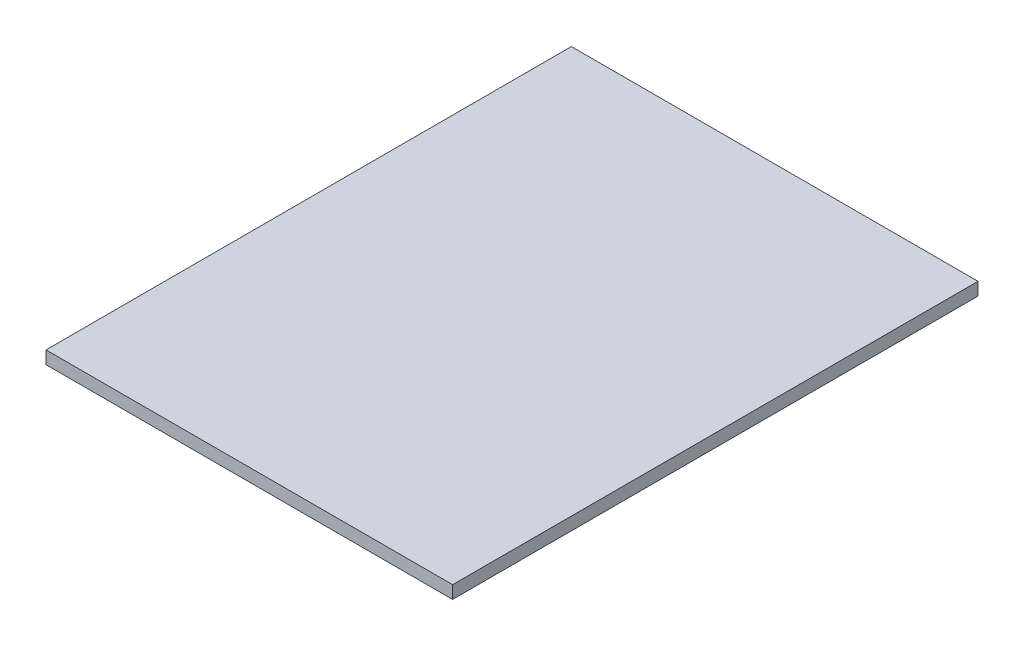
SolidWorks part; units mm, degrees
ref_plane "Front Plane" through (0, 0, 0) normal (0, 0, 1) x (1, 0, 0)
ref_plane "Top Plane" through (0, 0, 0) normal (0, 1, 0) x (1, 0, 0)
ref_plane "Right Plane" through (0, 0, 0) normal (1, 0, 0) x (0, 0, -1)
sketch "Sketch1" plane through (0, 0, 0) normal (0, 1, 0) x (1, 0, 0)
  line L0 (-6.35, 8.205) -> (6.35, -8.205) construction
  line L1 (-6.35, 8.205) -> (6.35, 8.205)
  line L2 (-6.35, 8.205) -> (-6.35, -8.205)
  line L3 (-6.35, -8.205) -> (6.35, -8.205)
  line L4 (6.35, 8.205) -> (6.35, -8.205)
  dimension "D1" = 12.7
  dimension "D2" = 16.41
extrude "Boss-Extrude1" add sketch "Sketch1" along normal blind 0.4
